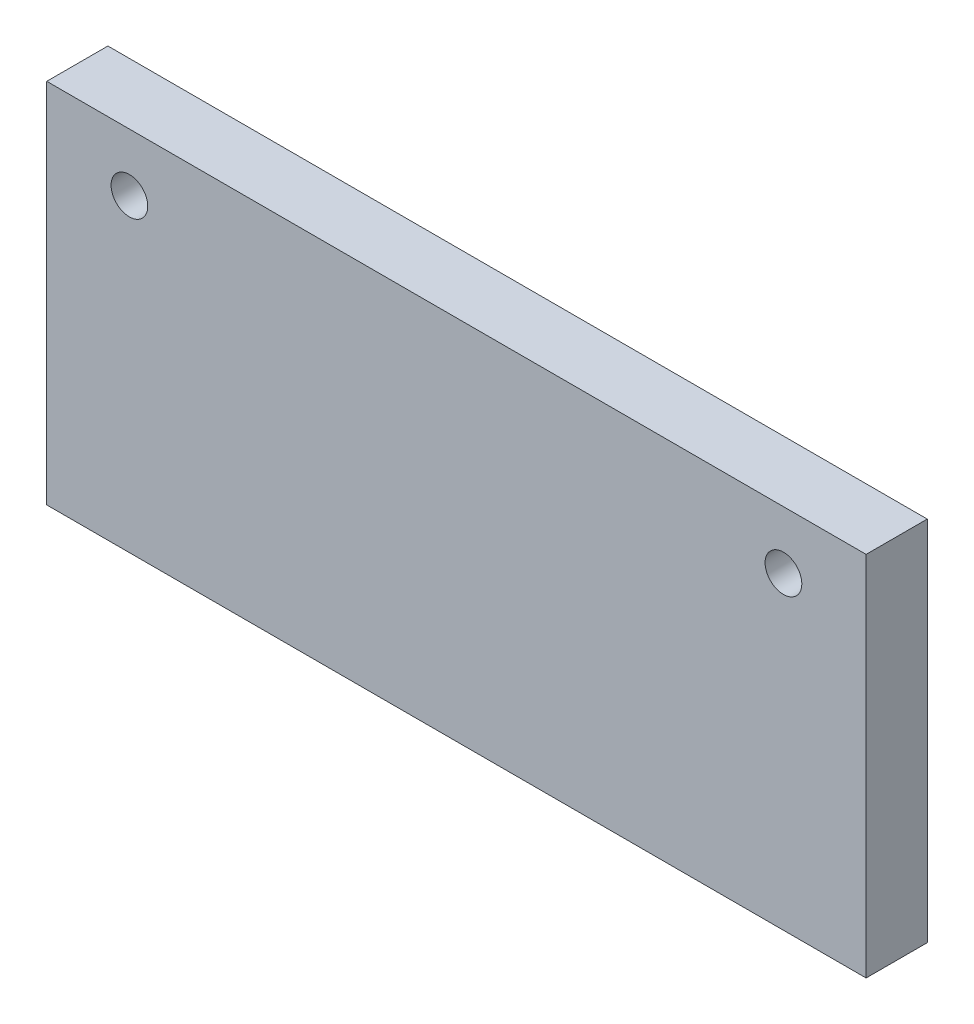
SolidWorks part; units mm, degrees
ref_plane "Alzado" through (0, 0, 0) normal (0, 0, 1) x (1, 0, 0)
ref_plane "Planta" through (0, 0, 0) normal (0, 1, 0) x (1, 0, 0)
ref_plane "Vista lateral" through (0, 0, 0) normal (1, 0, 0) x (0, 0, -1)
sketch "Croquis1" plane through (0, 0, 0) normal (0, 0, 1) x (1, 0, 0)
  line L0 (67, 60) -> (67, 0) construction
  line L1 (0, 0) -> (134, 0)
  line L2 (0, 0) -> (0, 60)
  line L3 (0, 60) -> (134, 60)
  line L4 (134, 0) -> (134, 60)
  circle A0 centre (13.5187, 50.5566) radius 3
  circle A1 centre (120.4813, 50.5566) radius 3
  dimension "D1" = 60
  dimension "D2" = 134
extrude "Saliente-Extruir1" add sketch "Croquis1" along normal blind 10
sketch "Croquis2" plane through (0, 0, 10) normal (0, 0, 1) x (1, 0, 0)
